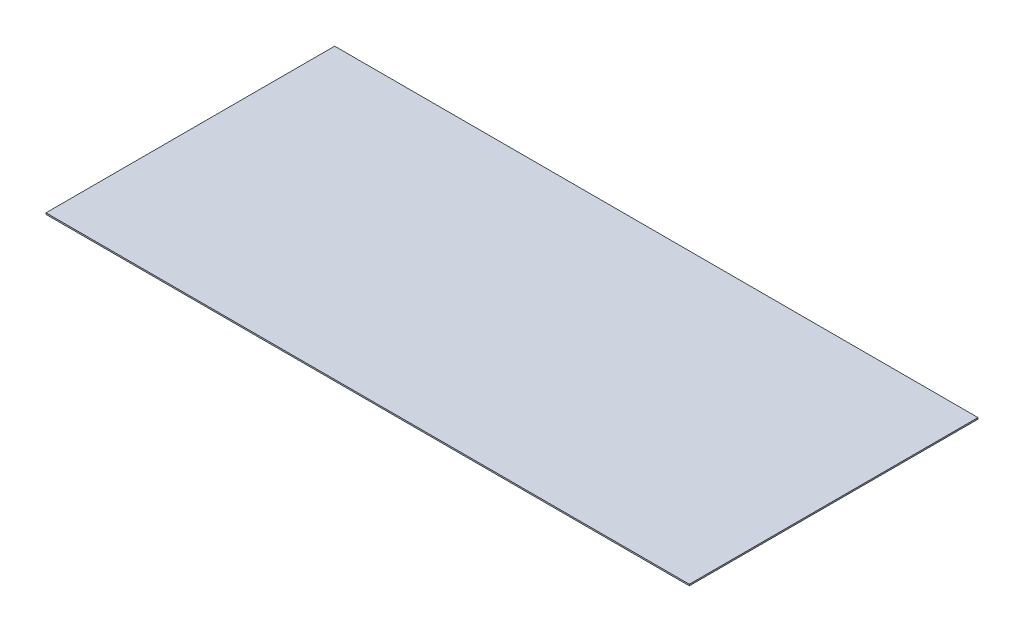
SolidWorks part; units mm, degrees
ref_plane "Front Plane" through (0, 0, 0) normal (0, 0, 1) x (1, 0, 0)
ref_plane "Top Plane" through (0, 0, 0) normal (0, 1, 0) x (1, 0, 0)
ref_plane "Right Plane" through (0, 0, 0) normal (1, 0, 0) x (0, 0, -1)
sketch "Sketch1" plane through (0, 0, 0) normal (0, 1, 0) x (1, 0, 0)
  line L1 (368.0521, -7.7099) -> (513.5941, -7.7099)
  line L2 (7.1181, 314.3621) -> (7.1181, -7.7099)
  line L3 (7.1181, 314.3621) -> (724.9221, 314.3621)
  line L4 (7.1181, -7.7099) -> (368.0521, -7.7099)
  line L6 (513.5941, -7.7099) -> (724.9221, -7.7099)
  line L7 (724.9221, -7.7099) -> (724.9221, 314.3621)
  dimension "D1" = 322.072
  dimension "D2" = 360.934
  dimension "D3" = 145.542
  dimension "D4" = 211.328
extrude "Boss-Extrude1" add sketch "Sketch1" along normal blind 1.5875
